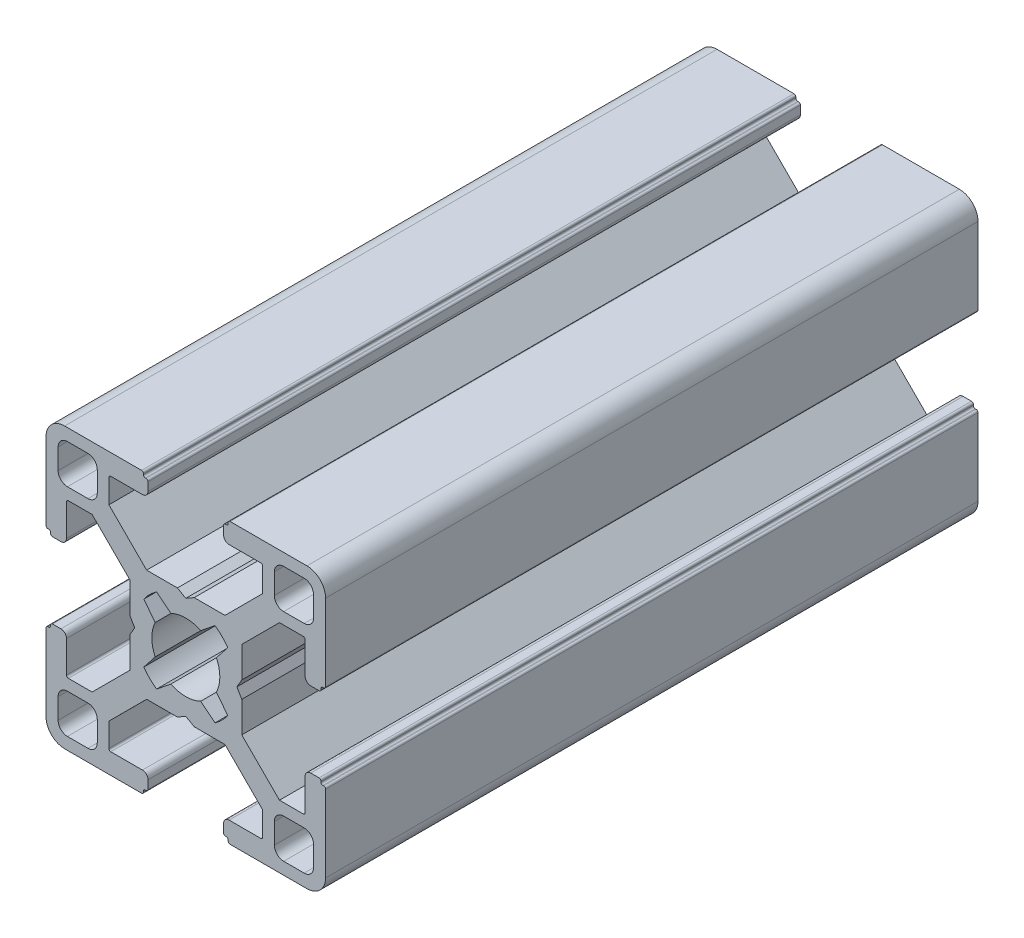
SolidWorks part; units mm, degrees
material "6061 Alloy"
ref_plane "Front" through (0, 0, 0) normal (0, 0, 1) x (1, 0, 0)
ref_plane "Top" through (0, 0, 0) normal (0, 1, 0) x (1, 0, 0)
ref_plane "Right" through (0, 0, 0) normal (1, 0, 0) x (0, 0, -1)
sketch "Sketch1" plane through (0, 0, 0) normal (0, 0, 1) x (1, 0, 0)
  line L0 (13.7, 12.7) -> (13.7, 10.5)
  line L1 (10.5, 9.5) -> (12.7, 9.5)
  line L2 (9.5, 12.7) -> (9.5, 10.5)
  line L3 (10.5, 13.7) -> (12.7, 13.7)
  line L4 (3.1359, 4.5184) -> (1.6001, 3.2806)
  line L5 (3.2806, 1.6001) -> (4.5053, 3.1547)
  line L6 (6.0045, 0.9) -> (5.4849, 0)
  line L7 (6.0045, 4.2045) -> (6.0045, 0.9)
  line L8 (0, -5.4849) -> (0.9, -6)
  line L9 (0.9, -6) -> (4.2045, -6)
  line L10 (4.2045, -6) -> (8.25, -10.05)
  line L11 (8.25, -10.05) -> (8.25, -12.6)
  line L12 (4.65, -12.8) -> (8.05, -12.8)
  line L13 (4.05, -14.3) -> (4.05, -13.4)
  line L14 (4.25, -14.5) -> (4.35, -14.5)
  line L15 (4.55, -14.8) -> (4.55, -14.7)
  line L16 (4.75, -15) -> (13, -15)
  line L17 (15, -13) -> (15, -4.75)
  line L18 (14.7, -4.55) -> (14.8, -4.55)
  line L19 (14.5, -4.35) -> (14.5, -4.25)
  line L20 (13.4, -4.05) -> (14.3, -4.05)
  line L21 (12.8, -8.05) -> (12.8, -4.65)
  line L22 (12.6, -8.25) -> (10.05, -8.25)
  line L23 (10.05, -8.25) -> (6.0045, -4.2045)
  line L24 (6.0045, -4.2045) -> (6.0045, -0.9)
  line L25 (6.0045, -0.9) -> (5.4849, 0)
  line L26 (10.05, 8.25) -> (6.0045, 4.2045)
  line L27 (12.6, 8.25) -> (10.05, 8.25)
  line L28 (12.8, 8.05) -> (12.8, 4.65)
  line L29 (13.4, 4.05) -> (14.3, 4.05)
  line L30 (14.5, 4.35) -> (14.5, 4.25)
  line L31 (14.7, 4.55) -> (14.8, 4.55)
  line L32 (15, 13) -> (15, 4.75)
  line L33 (4.75, 15) -> (13, 15)
  line L34 (4.55, 14.8) -> (4.55, 14.7)
  line L35 (4.25, 14.5) -> (4.35, 14.5)
  line L36 (4.05, 14.3) -> (4.05, 13.4)
  line L37 (4.65, 12.8) -> (8.05, 12.8)
  line L38 (8.25, 10.05) -> (8.25, 12.6)
  line L39 (4.2045, 6) -> (8.25, 10.05)
  line L40 (0.9, 6) -> (4.2045, 6)
  line L41 (0, 5.4849) -> (0.9, 6)
  line L42 (-13.7, -12.7) -> (-13.7, -10.5)
  line L43 (-10.5, -9.5) -> (-12.7, -9.5)
  line L44 (-9.5, -12.7) -> (-9.5, -10.5)
  line L45 (-10.5, -13.7) -> (-12.7, -13.7)
  line L46 (-3.1359, -4.5184) -> (-1.6001, -3.2806)
  line L47 (-3.2806, -1.6001) -> (-4.5053, -3.1547)
  line L48 (0, 5.4849) -> (-0.9, 6)
  line L49 (-0.9, 6) -> (-4.2045, 6)
  line L50 (-4.2045, 6) -> (-8.25, 10.05)
  line L51 (-8.25, 10.05) -> (-8.25, 12.6)
  line L52 (-4.65, 12.8) -> (-8.05, 12.8)
  line L53 (-4.05, 14.3) -> (-4.05, 13.4)
  line L54 (-4.25, 14.5) -> (-4.35, 14.5)
  line L55 (-4.55, 14.8) -> (-4.55, 14.7)
  line L56 (-4.75, 15) -> (-13, 15)
  line L57 (-15, 13) -> (-15, 4.75)
  line L58 (-14.7, 4.55) -> (-14.8, 4.55)
  line L59 (-14.5, 4.35) -> (-14.5, 4.25)
  line L60 (-13.4, 4.05) -> (-14.3, 4.05)
  line L61 (-12.8, 8.05) -> (-12.8, 4.65)
  line L62 (-12.6, 8.25) -> (-10.05, 8.25)
  line L63 (-10.05, 8.25) -> (-6.0045, 4.2045)
  line L64 (-6.0045, -0.9) -> (-5.4849, 0)
  line L65 (-6.0045, -4.2045) -> (-6.0045, -0.9)
  line L66 (-10.05, -8.25) -> (-6.0045, -4.2045)
  line L67 (-12.6, -8.25) -> (-10.05, -8.25)
  line L68 (-12.8, -8.05) -> (-12.8, -4.65)
  line L69 (-13.4, -4.05) -> (-14.3, -4.05)
  line L70 (-14.5, -4.35) -> (-14.5, -4.25)
  line L71 (-14.7, -4.55) -> (-14.8, -4.55)
  line L72 (-15, -13) -> (-15, -4.75)
  line L73 (-4.75, -15) -> (-13, -15)
  line L74 (-4.55, -14.8) -> (-4.55, -14.7)
  line L75 (-4.25, -14.5) -> (-4.35, -14.5)
  line L76 (-4.05, -14.3) -> (-4.05, -13.4)
  line L77 (3.2806, -1.6001) -> (4.5053, -3.1547)
  line L78 (3.1359, -4.5184) -> (1.6001, -3.2806)
  line L79 (-4.65, -12.8) -> (-8.05, -12.8)
  line L80 (-8.25, -10.05) -> (-8.25, -12.6)
  line L81 (-4.2045, -6) -> (-8.25, -10.05)
  line L82 (-0.9, -6) -> (-4.2045, -6)
  line L83 (0, -5.4849) -> (-0.9, -6)
  line L84 (10.5, -13.7) -> (12.7, -13.7)
  line L85 (9.5, -12.7) -> (9.5, -10.5)
  line L86 (10.5, -9.5) -> (12.7, -9.5)
  line L87 (13.7, -12.7) -> (13.7, -10.5)
  line L88 (-6.0045, 4.2045) -> (-6.0045, 0.9)
  line L89 (-6.0045, 0.9) -> (-5.4849, 0)
  line L90 (-3.2806, 1.6001) -> (-4.5053, 3.1547)
  line L91 (-3.1359, 4.5184) -> (-1.6001, 3.2806)
  line L92 (-10.5, 13.7) -> (-12.7, 13.7)
  line L93 (-9.5, 12.7) -> (-9.5, 10.5)
  line L94 (-10.5, 9.5) -> (-12.7, 9.5)
  line L95 (-13.7, 12.7) -> (-13.7, 10.5)
  line L96 (-23.4857, 0) -> (20.9308, 0) construction
  line L97 (0, 17.9563) -> (0, -17.361) construction
  arc A0 (13.7, 12.7) -> (12.7, 13.7) centre (12.7, 12.7) ccw
  arc A1 (12.7, 9.5) -> (13.7, 10.5) centre (12.7, 10.5) ccw
  arc A2 (9.5, 10.5) -> (10.5, 9.5) centre (10.5, 10.5) ccw
  arc A3 (10.5, 13.7) -> (9.5, 12.7) centre (10.5, 12.7) ccw
  arc A4 (1.6001, 3.2806) -> (-1.6001, 3.2806) centre (0, 0) ccw
  arc A5 (8.25, -12.6) -> (8.05, -12.8) centre (8.05, -12.6) cw
  arc A6 (4.65, -12.8) -> (4.05, -13.4) centre (4.65, -13.4) ccw
  arc A7 (4.05, -14.3) -> (4.25, -14.5) centre (4.25, -14.3) ccw
  arc A8 (4.35, -14.5) -> (4.55, -14.7) centre (4.35, -14.7) cw
  arc A9 (4.55, -14.8) -> (4.75, -15) centre (4.75, -14.8) ccw
  arc A10 (13, -15) -> (15, -13) centre (13, -13) ccw
  arc A11 (15, -4.75) -> (14.8, -4.55) centre (14.8, -4.75) ccw
  arc A12 (14.7, -4.55) -> (14.5, -4.35) centre (14.7, -4.35) cw
  arc A13 (14.5, -4.25) -> (14.3, -4.05) centre (14.3, -4.25) ccw
  arc A14 (13.4, -4.05) -> (12.8, -4.65) centre (13.4, -4.65) ccw
  arc A15 (12.8, -8.05) -> (12.6, -8.25) centre (12.6, -8.05) cw
  arc A16 (4.5053, 3.1547) -> (3.1359, 4.5184) centre (0, 0) ccw
  arc A17 (12.8, 8.05) -> (12.6, 8.25) centre (12.6, 8.05) ccw
  arc A18 (13.4, 4.05) -> (12.8, 4.65) centre (13.4, 4.65) cw
  arc A19 (14.5, 4.25) -> (14.3, 4.05) centre (14.3, 4.25) cw
  arc A20 (14.7, 4.55) -> (14.5, 4.35) centre (14.7, 4.35) ccw
  arc A21 (15, 4.75) -> (14.8, 4.55) centre (14.8, 4.75) cw
  arc A22 (13, 15) -> (15, 13) centre (13, 13) cw
  arc A23 (4.55, 14.8) -> (4.75, 15) centre (4.75, 14.8) cw
  arc A24 (4.35, 14.5) -> (4.55, 14.7) centre (4.35, 14.7) ccw
  arc A25 (4.05, 14.3) -> (4.25, 14.5) centre (4.25, 14.3) cw
  arc A26 (4.65, 12.8) -> (4.05, 13.4) centre (4.65, 13.4) cw
  arc A27 (8.25, 12.6) -> (8.05, 12.8) centre (8.05, 12.6) ccw
  arc A28 (-13.7, -12.7) -> (-12.7, -13.7) centre (-12.7, -12.7) ccw
  arc A29 (-12.7, -9.5) -> (-13.7, -10.5) centre (-12.7, -10.5) ccw
  arc A30 (-9.5, -10.5) -> (-10.5, -9.5) centre (-10.5, -10.5) ccw
  arc A31 (-10.5, -13.7) -> (-9.5, -12.7) centre (-10.5, -12.7) ccw
  arc A32 (-4.5053, -3.1547) -> (-3.1359, -4.5184) centre (0, 0) ccw
  arc A33 (-3.2806, 1.6001) -> (-3.2806, -1.6001) centre (0, 0) ccw
  arc A34 (-8.25, 12.6) -> (-8.05, 12.8) centre (-8.05, 12.6) cw
  arc A35 (-4.65, 12.8) -> (-4.05, 13.4) centre (-4.65, 13.4) ccw
  arc A36 (-4.05, 14.3) -> (-4.25, 14.5) centre (-4.25, 14.3) ccw
  arc A37 (-4.35, 14.5) -> (-4.55, 14.7) centre (-4.35, 14.7) cw
  arc A38 (-4.55, 14.8) -> (-4.75, 15) centre (-4.75, 14.8) ccw
  arc A39 (-13, 15) -> (-15, 13) centre (-13, 13) ccw
  arc A40 (-15, 4.75) -> (-14.8, 4.55) centre (-14.8, 4.75) ccw
  arc A41 (-14.7, 4.55) -> (-14.5, 4.35) centre (-14.7, 4.35) cw
  arc A42 (-14.5, 4.25) -> (-14.3, 4.05) centre (-14.3, 4.25) ccw
  arc A43 (-13.4, 4.05) -> (-12.8, 4.65) centre (-13.4, 4.65) ccw
  arc A44 (-12.8, 8.05) -> (-12.6, 8.25) centre (-12.6, 8.05) cw
  arc A45 (-4.5053, 3.1547) -> (-3.1359, 4.5184) centre (0, 0) cw
  arc A46 (-12.8, -8.05) -> (-12.6, -8.25) centre (-12.6, -8.05) ccw
  arc A47 (-13.4, -4.05) -> (-12.8, -4.65) centre (-13.4, -4.65) cw
  arc A48 (-14.5, -4.25) -> (-14.3, -4.05) centre (-14.3, -4.25) cw
  arc A49 (3.2806, 1.6001) -> (3.2806, -1.6001) centre (0, 0) cw
  arc A50 (4.5053, -3.1547) -> (3.1359, -4.5184) centre (0, 0) cw
  arc A51 (1.6001, -3.2806) -> (-1.6001, -3.2806) centre (0, 0) cw
  arc A52 (-14.7, -4.55) -> (-14.5, -4.35) centre (-14.7, -4.35) ccw
  arc A53 (-15, -4.75) -> (-14.8, -4.55) centre (-14.8, -4.75) cw
  arc A54 (-13, -15) -> (-15, -13) centre (-13, -13) cw
  arc A55 (-4.55, -14.8) -> (-4.75, -15) centre (-4.75, -14.8) cw
  arc A56 (10.5, -13.7) -> (9.5, -12.7) centre (10.5, -12.7) cw
  arc A57 (9.5, -10.5) -> (10.5, -9.5) centre (10.5, -10.5) cw
  arc A58 (12.7, -9.5) -> (13.7, -10.5) centre (12.7, -10.5) cw
  arc A59 (13.7, -12.7) -> (12.7, -13.7) centre (12.7, -12.7) cw
  arc A60 (-4.35, -14.5) -> (-4.55, -14.7) centre (-4.35, -14.7) ccw
  arc A61 (-4.05, -14.3) -> (-4.25, -14.5) centre (-4.25, -14.3) cw
  arc A62 (-4.65, -12.8) -> (-4.05, -13.4) centre (-4.65, -13.4) cw
  arc A63 (-8.25, -12.6) -> (-8.05, -12.8) centre (-8.05, -12.6) ccw
  arc A64 (-10.5, 13.7) -> (-9.5, 12.7) centre (-10.5, 12.7) cw
  arc A65 (-9.5, 10.5) -> (-10.5, 9.5) centre (-10.5, 10.5) cw
  arc A66 (-12.7, 9.5) -> (-13.7, 10.5) centre (-12.7, 10.5) cw
  arc A67 (-13.7, 12.7) -> (-12.7, 13.7) centre (-12.7, 12.7) cw
  point P81 (15, 15)
  point P82 (0, 15)
  point P203 (0, -15)
  point P204 (15, -15)
  point P206 (0, 0)
  point P207 (15, 0)
  point P219 (-15, 0)
  point P220 (-15, -15)
  point P221 (-15, 15)
extrude "Base-Extrude" add sketch "Sketch1" against normal blind 70
